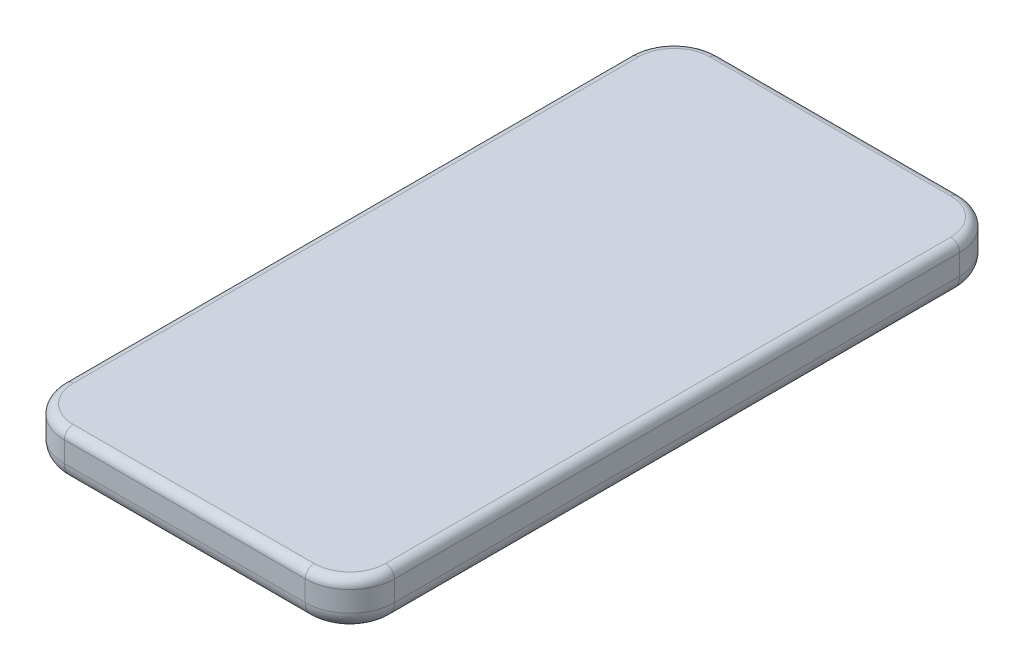
SolidWorks part; units mm, degrees
ref_plane "前视基准面" through (0, 0, 0) normal (0, 0, 1) x (1, 0, 0)
ref_plane "上视基准面" through (0, 0, 0) normal (0, 1, 0) x (1, 0, 0)
ref_plane "右视基准面" through (0, 0, 0) normal (1, 0, 0) x (0, 0, -1)
sketch "草图1" plane through (0, 0, 0) normal (0, 1, 0) x (1, 0, 0)
  line L0 (-37, 0) -> (37, 0)
  line L1 (37, 0) -> (37, -146.7)
  line L2 (37, -146.7) -> (-37, -146.7)
  line L3 (-37, -146.7) -> (-37, 0)
  point P4 (0, 0)
  dimension "D1" = 74
  dimension "D2" = 146.7
extrude "凸台-拉伸1" add sketch "草图1" along normal blind 10.6
fillet "圆角1" radius 10 4 edges at (37, 5.3, 146.7) (-37, 5.3, 146.7) (-37, 5.3, 0) (37, 5.3, 0)
fillet "圆角2" radius 4 8 edges at (-34.0711, 0, 2.9289) (0, 0, 0) (34.0711, 0, 2.9289) (37, 0, 73.35) (34.0711, 0, 143.7711) (0, 0, 146.7) (-34.0711, 0, 143.7711) (-37, 0, 73.35)
fillet "圆角3" radius 2 8 edges at (-37, 10.6, 73.35) (-34.0711, 10.6, 2.9289) (0, 10.6, 0) (34.0711, 10.6, 2.9289) (37, 10.6, 73.35) (34.0711, 10.6, 143.7711) (0, 10.6, 146.7) (-34.0711, 10.6, 143.7711)
sketch "草图2" plane through (0, 0, 0) normal (0, -1, 0) x (1, 0, 0)
  line L0 (0, 146.7) -> (0, 0) construction
  line L1 (-27, 146.7) -> (27, 146.7) construction
  line L2 (27, 0) -> (-27, 0) construction
  circle A0 centre (0, 72.4) radius 28
  dimension "D1" = 56
  dimension "D2" = 72.4
